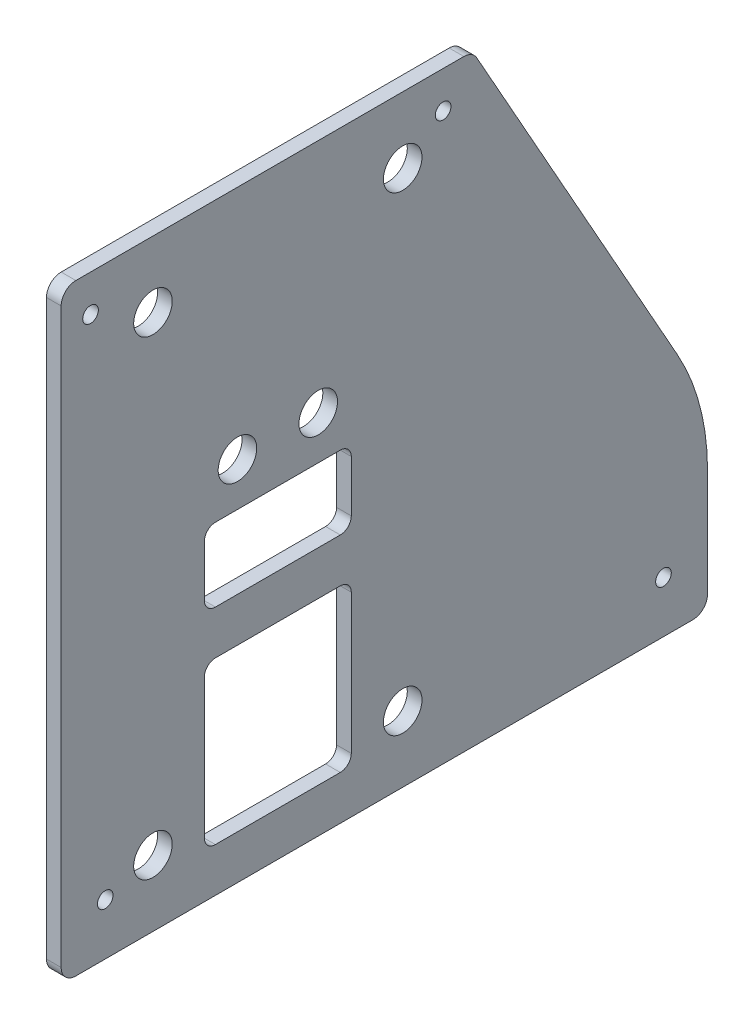
SolidWorks part; units mm, degrees
material "PE High Density"
ref_plane "Front Plane" through (0, 0, 0) normal (0, 0, 1) x (1, 0, 0)
ref_plane "Top Plane" through (0, 0, 0) normal (0, 1, 0) x (1, 0, 0)
ref_plane "Right Plane" through (0, 0, 0) normal (1, 0, 0) x (0, 0, -1)
sketch "Sketch1" plane through (0, 0, 0) normal (1, 0, 0) x (0, 0, -1)
  line L0 (0, 0) -> (-279.4, 0) construction
  line L1 (-279.4, 0) -> (-279.4, 257.175)
  line L2 (-279.4, 257.175) -> (-101.6, 257.175)
  line L3 (-101.6, 257.175) -> (0, 76.2)
  line L4 (0, 76.2) -> (0, 0)
  line L5 (-279.4, 0) -> (-279.4, -3.175)
  line L6 (-279.4, -3.175) -> (-279.4, -41.275) construction
  line L7 (-279.4, -41.275) -> (0, -41.275) construction
  line L8 (0, -41.275) -> (0, -3.175) construction
  line L9 (0, -3.175) -> (0, 0)
  line L10 (-279.4, -3.175) -> (0, -3.175)
  line L11 (-99.8175, 254) -> (-279.4, 254) construction
  dimension "D1" = 254
  dimension "D2" = 76.2
  dimension "D3" = 279.4
  dimension "D4" = 3.175
  dimension "D5" = 38.1
  dimension "D6" = 177.8
  dimension "D7" = 3.175
extrude "Boss-Extrude1" add sketch "Sketch1" along normal blind 6.35
sketch "Sketch16" plane through (6.35, 0, 0) normal (1, 0, 0) x (0, 0, -1)
  line L0 (-279.4, 257.175) -> (-279.4, -3.175) construction
  line L1 (-101.6, 257.175) -> (-279.4, 257.175) construction
  point P0 (-266.7, 241.3)
  point P1 (-114.3, 241.3)
  dimension "D1" = 12.7
  dimension "D2" = 152.4
  dimension "D3" = 15.875
hole_wizard "1/4 Clearance Hole4" positions "Sketch17" profile "Sketch18" hole size "1/4" standard "ANSI Inch" end condition through all
sketch "Sketch17" plane through (6.35, 0, 0) normal (1, 0, 0) x (0, 0, -1)
  point P0 (-266.7, 241.3)
  point P3 (-114.3, 241.3)
sketch "Sketch18" plane through (6.35, 241.3, 266.7) normal (0, 1, 0) x (0, 0, -1)
  line L0 (0, 0) -> (0, 6.35)
  line L1 (0, 6.35) -> (3.3782, 6.35)
  line L2 (3.3782, 6.35) -> (3.3782, 0)
  line L5 (3.3782, 0) -> (0, 0)
  line L11 (0, -6.35) -> (0, 107.95) construction
  dimension "Thru Hole Dia." = 6.7564
  dimension "Thru Hole Depth" = 6.35
sketch "Sketch19" plane through (0, 0, 0) normal (-1, 0, 0) x (0, 0, 1)
  line L0 (279.4, 19.05) -> (0, 19.05) construction
  line L1 (279.4, 257.175) -> (279.4, -3.175) construction
  line L2 (0, -3.175) -> (0, 76.2) construction
  point P8 (19.05, 19.05)
  point P9 (260.35, 19.05)
  point P10 (111.125, 19.05)
  dimension "D1" = 19.05
  dimension "D2" = 19.05
  dimension "D3" = 92.075
  dimension "D4" = 19.05
hole_wizard "1/4 Clearance Hole5" positions "Sketch20" profile "Sketch21" hole size "1/4" standard "ANSI Inch" end condition through all
sketch "Sketch20" plane through (0, 0, 0) normal (-1, 0, 0) x (0, 0, 1)
  point P0 (19.05, 19.05)
  point P6 (260.35, 19.05)
sketch "Sketch21" plane through (0, 19.05, 19.05) normal (0, 1, 0) x (0, 0, 1)
  line L0 (0, 0) -> (0, 6.35)
  line L1 (0, 6.35) -> (3.3782, 6.35)
  line L2 (3.3782, 6.35) -> (3.3782, 0)
  line L5 (3.3782, 0) -> (0, 0)
  line L11 (0, -6.35) -> (0, 107.95) construction
  dimension "Thru Hole Dia." = 6.7564
  dimension "Thru Hole Depth" = 6.35
fillet "Fillet4" radius 101.6 1 edges at (3.175, 76.2, 0)
sketch "Sketch22" plane through (6.35, 0, 0) normal (1, 0, 0) x (0, 0, -1)
  line L0 (0, 0) -> (-279.4, 0) construction
  line L1 (-279.4, 257.175) -> (-279.4, -3.175) construction
  line L2 (-185.7375, 136.525) -> (-185.7375, 15.875) construction
  line L3 (-217.4875, 15.875) -> (-153.9875, 15.875)
  line L4 (-217.4875, 15.875) -> (-217.4875, 85.725)
  line L5 (-217.4875, 85.725) -> (-153.9875, 85.725)
  line L6 (-153.9875, 15.875) -> (-153.9875, 85.725)
  line L7 (-217.4875, 104.775) -> (-153.9875, 104.775)
  line L8 (-217.4875, 104.775) -> (-217.4875, 136.525)
  line L9 (-217.4875, 136.525) -> (-153.9875, 136.525)
  line L10 (-153.9875, 104.775) -> (-153.9875, 136.525)
  line L11 (0, -3.175) -> (0, 49.631) construction
  line L12 (-185.7375, 136.525) -> (-185.7375, 155.325) construction
  line L13 (-203.2, 155.325) -> (-168.275, 155.325) construction
  line L14 (-217.4875, 120.65) -> (-153.9875, 120.65) construction
  point P20 (-185.7375, 155.325)
  dimension "D1" = 19.05
  dimension "D2" = 69.85
  dimension "D3" = 15.875
  dimension "D4" = 63.5
  dimension "D5" = 185.7375
  dimension "D6" = 31.75
  dimension "D7" = 18.8
  dimension "D8" = 34.925
extrude "Cut-Extrude1" cut sketch "Sketch22" against normal through all
sketch "Sketch23" plane through (6.35, 0, 0) normal (1, 0, 0) x (0, 0, -1)
  line L0 (-239.7125, 25.4) -> (-131.7625, 25.4) construction
  line L1 (-217.4875, 50.8) -> (-153.9875, 50.8) construction
  line L2 (-239.7125, 228.6) -> (-131.7625, 228.6) construction
  line L3 (-217.4875, 85.725) -> (-217.4875, 15.875) construction
  line L4 (-185.7375, 25.4) -> (-185.7375, 228.6) construction
  line L5 (-153.9875, 15.875) -> (-153.9875, 85.725) construction
  line L6 (-217.4875, 15.875) -> (-153.9875, 15.875) construction
  line L7 (-217.4875, 136.525) -> (-217.4875, 104.775) construction
  line L8 (-217.4875, 120.65) -> (-153.9875, 120.65) construction
  line L9 (-153.9875, 104.775) -> (-153.9875, 136.525) construction
  line L10 (-203.2, 155.325) -> (-168.275, 155.325) construction
  line L11 (-153.9875, 15.875) -> (-153.9875, 85.725) construction
  line L12 (-217.4875, 15.875) -> (-217.4875, 85.725) construction
  line L13 (-153.9875, 136.525) -> (-217.4875, 136.525) construction
  point P18 (-185.7375, 50.8)
  point P28 (-185.7375, 155.325)
  dimension "D1" = 9.525
  dimension "D2" = 53.975
  dimension "D3" = 203.2
  dimension "D4" = 22.225
  dimension "D5" = 22.225
  dimension "D6" = 18.8
  dimension "D7" = 34.925
hole_wizard "5/8 Clearance Hole1" positions "Sketch24" profile "Sketch25" hole size "5/8" standard "ANSI Inch" end condition through all
sketch "Sketch24" plane through (6.35, 0, 0) normal (1, 0, 0) x (0, 0, -1)
  point P0 (-239.7125, 228.6)
  point P3 (-131.7625, 228.6)
  point P6 (-239.7125, 25.4)
  point P9 (-131.7625, 25.4)
  point P12 (-203.2, 155.325)
  point P14 (-168.275, 155.325)
sketch "Sketch25" plane through (6.35, 228.6, 239.7125) normal (0, 1, 0) x (0, 0, -1)
  line L0 (0, 0) -> (0, 6.35)
  line L1 (0, 6.35) -> (8.3337, 6.35)
  line L2 (8.3337, 6.35) -> (8.3337, 0)
  line L5 (8.3337, 0) -> (0, 0)
  line L11 (0, -6.35) -> (0, 107.95) construction
  dimension "Thru Hole Dia." = 16.6675
  dimension "Thru Hole Depth" = 6.35
fillet "Fillet5" radius 6.35 4 edges at (3.175, -3.175, 279.4) (3.175, 257.175, 279.4) (3.175, 257.175, 101.6) (3.175, -3.175, 0)
fillet "Fillet6" radius 4.7625 8 edges at (3.175, 15.875, 153.9875) (3.175, 104.775, 153.9875) (3.175, 85.725, 153.9875) (3.175, 136.525, 153.9875) (3.175, 85.725, 217.4875) (3.175, 136.525, 217.4875) (3.175, 15.875, 217.4875) (3.175, 104.775, 217.4875)
